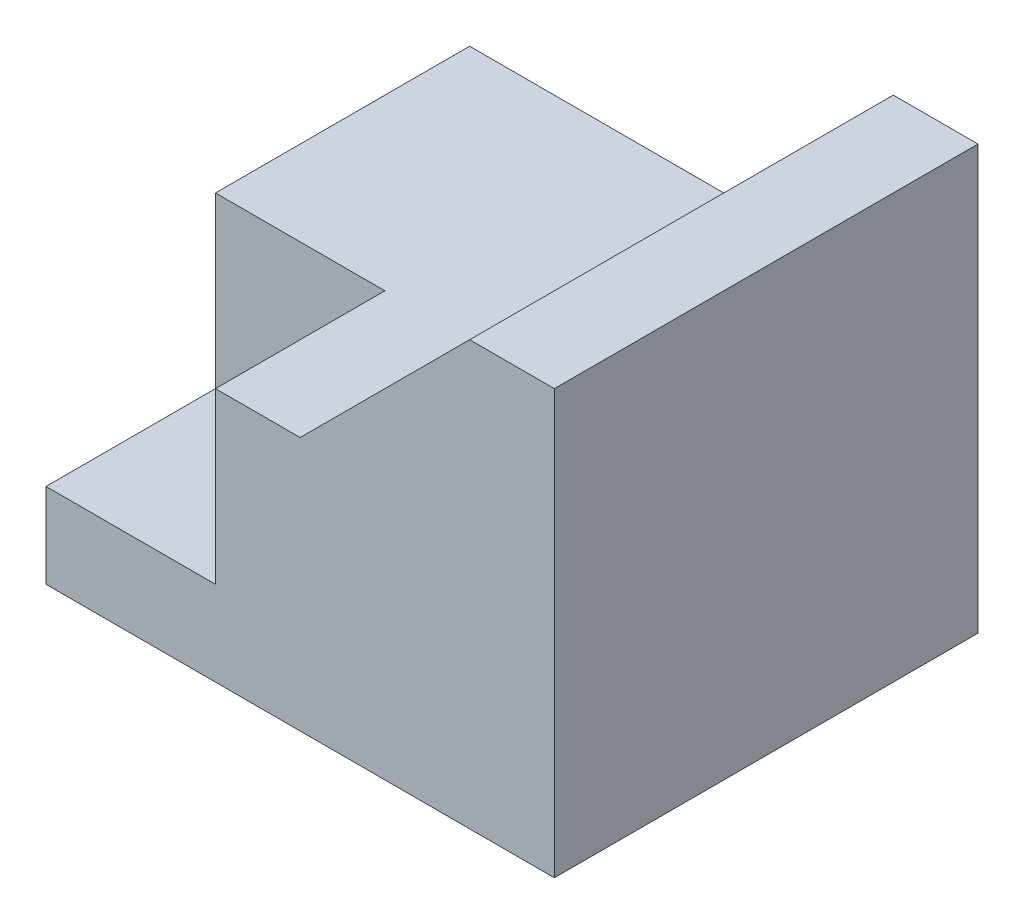
SolidWorks part; units mm, degrees
ref_plane "Front Plane" through (0, 0, 0) normal (0, 0, 1) x (1, 0, 0)
ref_plane "Top Plane" through (0, 0, 0) normal (0, 1, 0) x (1, 0, 0)
ref_plane "Right Plane" through (0, 0, 0) normal (1, 0, 0) x (0, 0, -1)
sketch "Sketch1" plane through (0, 0, 0) normal (0, 0, 1) x (1, 0, 0)
  line L0 (0, 0) -> (0, 30)
  line L1 (0, 30) -> (30, 30)
  line L2 (30, 30) -> (50, 50)
  line L3 (50, 50) -> (60, 50)
  line L4 (60, 50) -> (60, 0)
  line L5 (60, 0) -> (0, 0)
  dimension "D1" = 60
  dimension "D2" = 30
  dimension "D3" = 30
  dimension "D4" = 50
  dimension "D5" = 10
extrude "Boss-Extrude2" add sketch "Sketch1" along normal blind 50
sketch "Sketch3" plane through (0, 0, 50) normal (0, 0, 1) x (1, 0, 0)
  line L1 (0, 30) -> (20, 30)
  line L2 (0, 30) -> (0, 10)
  line L3 (0, 10) -> (20, 10)
  line L4 (20, 30) -> (20, 10)
  dimension "D1" = 20
  dimension "D2" = 20
extrude "Cut-Extrude2" cut sketch "Sketch3" against normal blind 20
